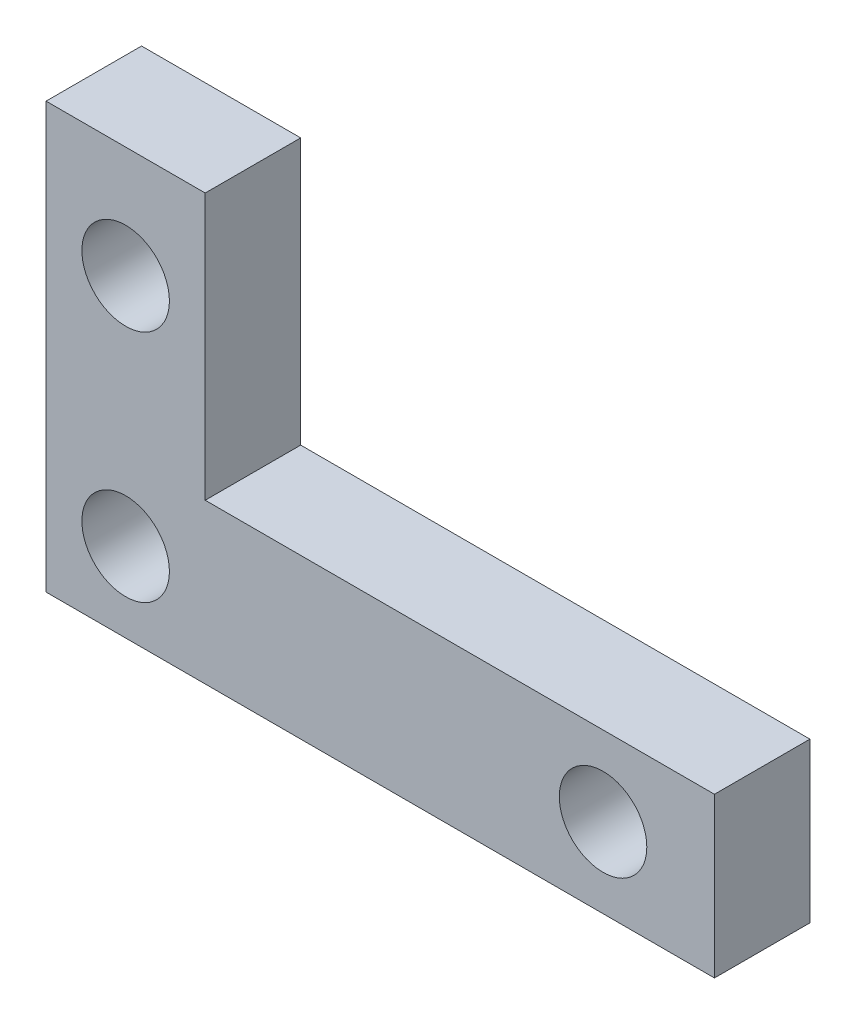
SolidWorks part; units mm, degrees
ref_plane "Front Plane" through (0, 0, 0) normal (0, 0, 1) x (1, 0, 0)
ref_plane "Top Plane" through (0, 0, 0) normal (0, 1, 0) x (1, 0, 0)
ref_plane "Right Plane" through (0, 0, 0) normal (1, 0, 0) x (0, 0, -1)
sketch "Sketch1" plane through (0, 0, 0) normal (0, 0, 1) x (1, 0, 0)
  line L0 (0, 0) -> (21, 0)
  line L1 (21, 0) -> (21, 5)
  line L2 (21, 5) -> (5, 5)
  line L3 (5, 5) -> (5, 13.36)
  line L4 (5, 13.36) -> (0, 13.36)
  line L5 (0, 13.36) -> (0, 0)
  circle A0 centre (17.5, 2.5) radius 1.375
  circle A1 centre (2.5, 2.5) radius 1.375
  circle A3 centre (2.5, 9.86) radius 1.375
  dimension "D5" = 2.75
  dimension "D6" = 2.75
  dimension "D7" = 2.75
  dimension "D10" = 7.36
  dimension "D12" = 15
  dimension "D2" = 2.5
  dimension "D3" = 5
  dimension "D4" = 5
  dimension "D8" = 3.5
  dimension "D9" = 3.5
  dimension "D11" = 2.5
extrude "Boss-Extrude1" add sketch "Sketch1" along normal blind 3
